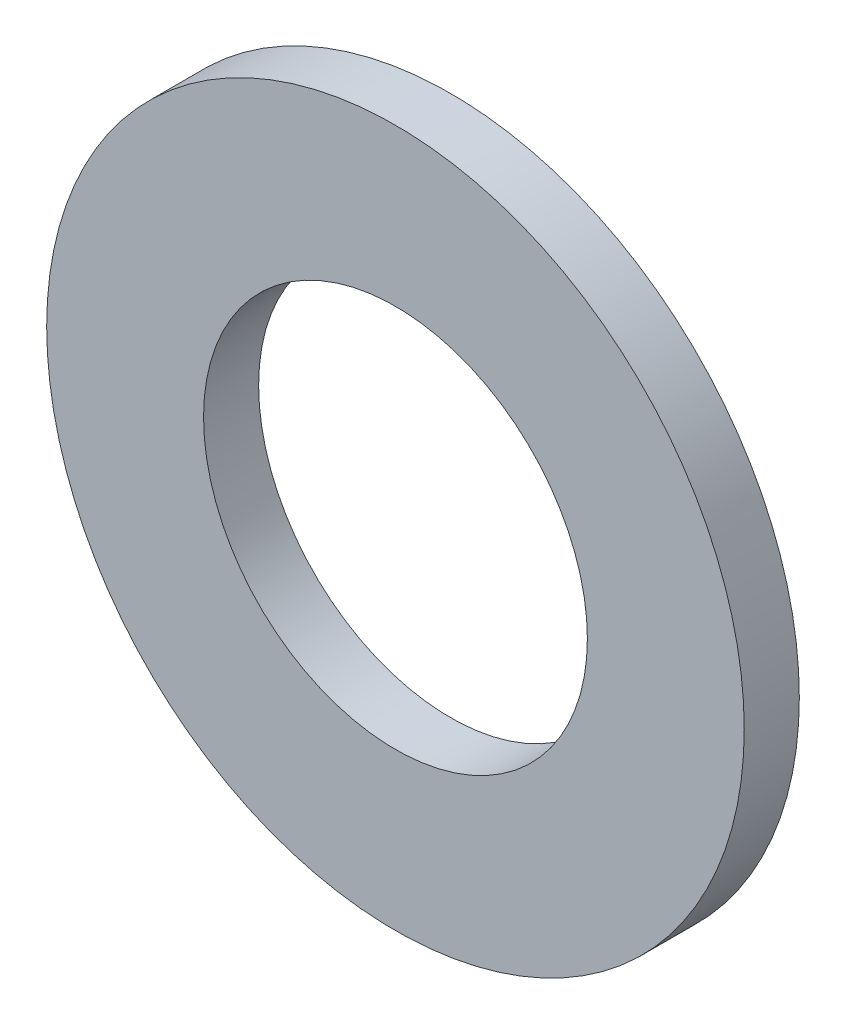
SolidWorks part; units mm, degrees
ref_plane "Front Plane" through (0, 0, 0) normal (0, 0, 1) x (1, 0, 0)
ref_plane "Top Plane" through (0, 0, 0) normal (0, 1, 0) x (1, 0, 0)
ref_plane "Right Plane" through (0, 0, 0) normal (1, 0, 0) x (0, 0, -1)
sketch "Sketch1" plane through (0, 0, 0) normal (0, 0, 1) x (1, 0, 0)
  line L0 (-2.6543, 0) -> (2.6543, 0) construction
  line L1 (0, -2.6543) -> (0, 2.6543) construction
  circle A0 centre (0, 0) radius 2.6543
  circle A1 centre (0, 0) radius 1.4605
  point P4 (0, 0)
  point P9 (0, 0)
  dimension "ID" = 2.921
  dimension "OD" = 5.3086
sketch "Sketch2" plane through (0, 0, 0) normal (1, 0, 0) x (0, 0, -1)
  line L0 (0.2095, 2.6543) -> (-0.2095, 2.6543) construction
  line L1 (0, 2.6543) -> (0, -2.6543) construction
  point P4 (0, 2.6543)
  dimension "Thickness" = 0.4191
sketch "Sketch3" plane through (0, 0, 0) normal (0, 0, 1) x (1, 0, 0)
  line L0 (0, -2.6543) -> (0, 2.6543) construction
  circle A0 centre (0, 0) radius 2.6543
  circle A1 centre (0, 0) radius 1.4605
  circle A2 centre (0, 0) radius 1.4605 construction
extrude "Boss-Extrude1" add sketch "Sketch3" along normal mid plane 0.4191
equation "\"D1@Boss-Extrude1\" = \"Thickness@Sketch2\""
